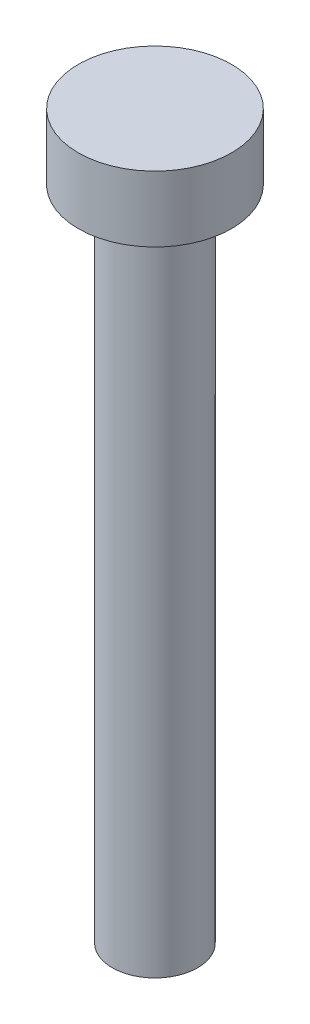
SolidWorks part; units mm, degrees
ref_plane "Front Plane" through (0, 0, 0) normal (0, 0, 1) x (1, 0, 0)
ref_plane "Top Plane" through (0, 0, 0) normal (0, 1, 0) x (1, 0, 0)
ref_plane "Right Plane" through (0, 0, 0) normal (1, 0, 0) x (0, 0, -1)
sketch "Sketch1" plane through (0, 0, 0) normal (0, 1, 0) x (1, 0, 0)
  circle A0 centre (0, 0) radius 3.5
  dimension "D1" = 7
extrude "Boss-Extrude1" add sketch "Sketch1" along normal blind 3
sketch "Sketch2" plane through (0, 0, 0) normal (0, -1, 0) x (1, 0, 0)
  circle A0 centre (0, 0) radius 1.95
  dimension "D1" = 3.9
extrude "Boss-Extrude2" add sketch "Sketch2" along normal blind 30
